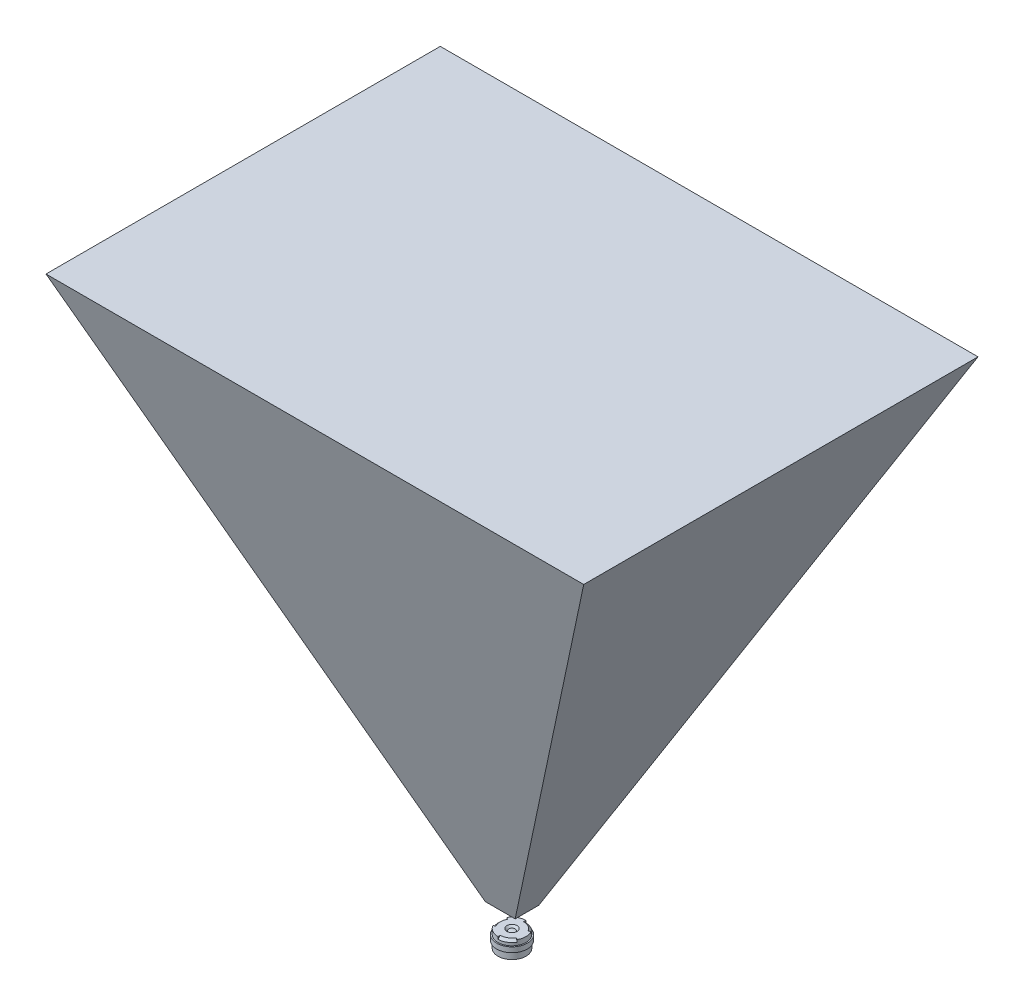
SolidWorks part; units mm, degrees
material "ABS PC"
ref_plane "Vorne" through (0, 0, 0) normal (0, 0, 1) x (1, 0, 0)
ref_plane "Oben" through (0, 0, 0) normal (0, 1, 0) x (1, 0, 0)
ref_plane "Rechts" through (0, 0, 0) normal (1, 0, 0) x (0, 0, -1)
sketch "Skizze3" plane through (0, 0, 0) normal (0, 0, 1) x (1, 0, 0)
  line L0 (0, 0) -> (0, -2.1568) construction
  line L1 (1, 0.8) -> (2.75, 0.8)
  line L2 (2.75, 0.8) -> (2.75, -2.55)
  line L3 (2.75, -2.55) -> (2.1, -2.55)
  line L4 (1, 0.8) -> (0.625, 0.425)
  line L5 (0.8125, 0.6125) -> (0.8125, 0.8) construction
  line L6 (0.8125, 0.8) -> (1, 0.8) construction
  line L7 (2.1, -2.55) -> (1.8, -2.25)
  line L8 (2.1, -2.55) -> (2.1, -2.4) construction
  line L9 (2.1, -2.4) -> (1.95, -2.4) construction
  line L10 (0, -2.55) -> (0, 0.525)
  arc A0 (1.8, -2.25) -> (0, -2.55) centre (0, 3) cw
  arc A1 (0, 0.525) -> (0.625, 0.425) centre (0, -1.4781) cw
  dimension "D6" = 0.1
  dimension "D1" = 3.35
  dimension "D2" = 5.5
  dimension "D3" = 2
  dimension "D4" = 1.25
  dimension "D5" = 3.6
  dimension "D7" = 0.8
  dimension "D8" = 0.3
revolve "Body" add sketch "Skizze3" angle 360 about L0
sketch "Skizze4" plane through (0, 0, 0) normal (0, 0, 1) x (1, 0, 0)
  line L0 (0, 0) -> (0, 1.3093) construction
  line L1 (2.75, -2.55) -> (2.75, 0.8) construction
  line L2 (2.75, -0.2) -> (3, -0.2)
  line L3 (2.75, -0.2) -> (2.75, -1.2)
  line L4 (2.75, -1.2) -> (3, -1.2)
  line L5 (3, -0.2) -> (3, -1.2)
  line L6 (2.75, 0.8) -> (-2.75, 0.8) construction
  dimension "D1" = 2
  dimension "D2" = 1
  dimension "D3" = 6
revolve "Thread" add sketch "Skizze4" angle 360 about L0
sketch "Skizze5" plane through (0, 0, 0) normal (1, 0, 0) x (0, 0, -1)
  line L0 (0, 0) -> (0, -3.7681) construction
  line L1 (2.75, 0.8) -> (2.75, 0.35)
  line L2 (2.75, -0.2) -> (2.75, 0.8) construction
  line L3 (2.75, 0.35) -> (2.3, 0.8)
  line L4 (2.75, 0.8) -> (-2.75, 0.8) construction
  line L5 (2.3, 0.8) -> (2.75, 0.8)
  dimension "D1" = 0.45
revolve "Toolface" cut sketch "Skizze5" angle 60 about L0
pattern_circular "Kreismuster1" count 3 over 360 about axis through (0, 0, 0) along (0, 1, 0) of "Toolface"
sketch "Skizze6" plane through (0, 0, 0) normal (1, 0, 0) x (0, 0, -1)
  line L0 (0, 0) -> (0, 10.2784) construction
  line L1 (-2.3112, 5.0578) -> (-38.7082, 105.0578)
  line L2 (-38.7082, 105.0578) -> (38.7082, 105.0578)
  line L3 (-2.3112, 5.0578) -> (2.3112, 5.0578)
  line L4 (0, 105.0578) -> (0, 5.0578) construction
  line L5 (-2.3112, 5.0578) -> (0, -1.2922) construction
  line L8 (2.3112, 5.0578) -> (38.7082, 105.0578)
  point P3 (-0.625, 0.425)
  dimension "D1" = 100
  dimension "D2" = 6.35
  dimension "D3" = 40
extrude "FOV - 3,6mm f/2,9" add sketch "Skizze6" along normal mid plane 200 separate body
sketch "Skizze8" plane through (0, 0, 0) normal (0, 0, 1) x (1, 0, 0)
  line L0 (0, 0) -> (0, 233.3089) construction
  line L1 (-2.9348, 5.0578) -> (-52.793, 105.0578)
  line L2 (100, 5.0578) -> (-100, 5.0578) construction
  line L3 (100, 105.0578) -> (-100, 105.0578) construction
  line L4 (-52.793, 105.0578) -> (52.793, 105.0578)
  line L5 (-2.9348, 5.0578) -> (2.9348, 5.0578)
  line L8 (2.9348, 5.0578) -> (52.793, 105.0578)
  circle A0 centre (0, 0) radius 5
  point P9 (-0.625, 0.425)
  point P16 (0, 5.0578)
  point P17 (0, 105.0578)
  dimension "D2" = 10
  dimension "D1" = 53
extrude "FOV2" cut sketch "Skizze8" against normal through all and the other way through all flip side to cut
